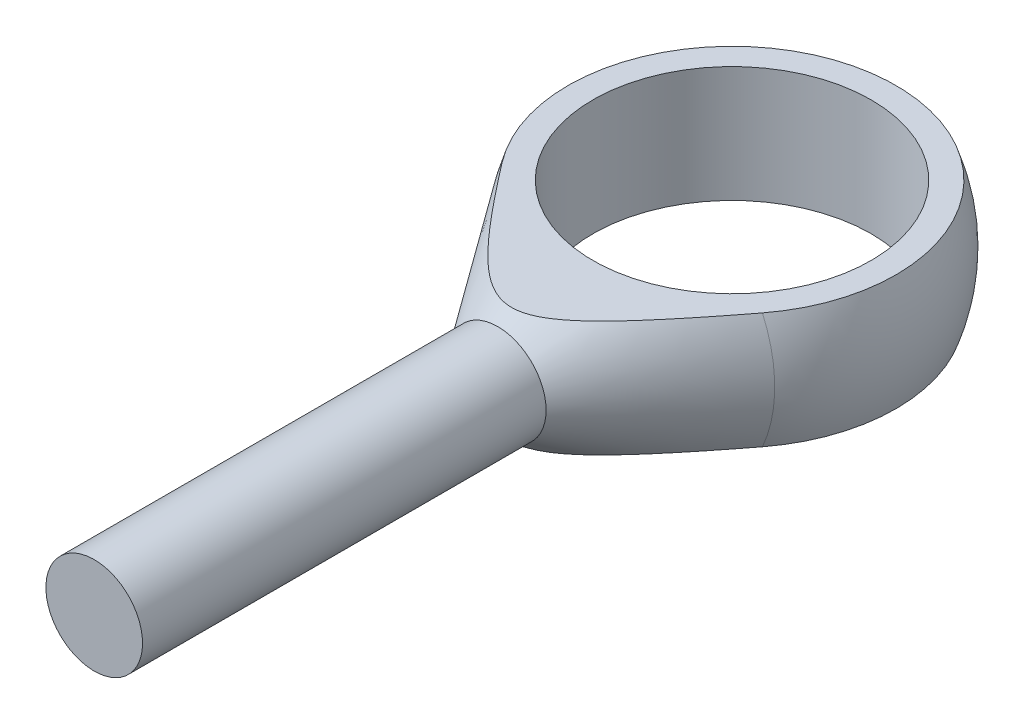
SolidWorks part; units mm, degrees
ref_plane "Front Plane" through (0, 0, 0) normal (0, 0, 1) x (1, 0, 0)
ref_plane "Top Plane" through (0, 0, 0) normal (0, 1, 0) x (1, 0, 0)
ref_plane "Right Plane" through (0, 0, 0) normal (1, 0, 0) x (0, 0, -1)
sketch "Sketch1" plane through (0, 0, 0) normal (0, 0, 1) x (1, 0, 0)
  line L0 (-8.4853, 3) -> (-7.2, 3)
  line L1 (-7.2, 3) -> (-7.2, -3)
  line L2 (-7.2, -3) -> (-8.4853, -3)
  line L3 (0, 0) -> (-7.2, 3) construction
  line L4 (0, -4.3877) -> (0, 5.0326) construction
  arc A0 (-8.4853, 3) -> (-8.4853, -3) centre (0, 0) ccw
  point P5 (-7.2, 0)
  dimension "D1" = 18
  dimension "D2" = 6
  dimension "D3" = 7.8
revolve "Revolve1" add sketch "Sketch1" angle 360 about L4
ref_plane "Plane1" through (0, 0, 0) normal (0, 1, 0) x (1, 0, 0)
sketch "Sketch3" plane through (0, 0, 0) normal (0, 1, 0) x (1, 0, 0)
  line L0 (0, 0) -> (0, -33) construction
  dimension "D1" = 33
ref_plane "Plane2" through (0, 0, 33) normal (0, 0, 1) x (1, 0, 0)
sketch "Sketch4" plane through (0, 0, 33) normal (0, 0, 1) x (1, 0, 0)
  circle A0 centre (0, 0) radius 2.5
  dimension "D1" = 5
extrude "Boss-Extrude1" add sketch "Sketch4" against normal up to surface (24.3542 mm away)
sketch "Sketch5" plane through (0, 0, 0) normal (0, 1, 0) x (1, 0, 0)
  line L0 (0, -7.8) -> (0, -15.691)
  line L1 (0, 0) -> (0, -33) construction
  line L2 (0, -15.691) -> (-7.3724, -5.1622)
  line L3 (-7.8, 0) -> (-9, 0)
  arc A0 (-9, 0) -> (-7.3724, -5.1622) centre (0, 0) ccw
  arc A1 (-7.8, 0) -> (0, -7.8) centre (0, 0) ccw
  dimension "D1" = 18
  dimension "D2" = 15.6
  dimension "D3" = 35
revolve "Revolve2" add sketch "Sketch5" angle 360 about L0
ref_plane "Plane3" through (0, 0, 0) normal (-1, 0, 0) x (0, 0, 1)
sketch "Sketch6" plane through (0, 0, 0) normal (-1, 0, 0) x (0, 0, 1)
  line L0 (0, 7.8) -> (0, 3) construction
  line L1 (0, 3) -> (11.4066, 3)
  line L2 (0, 3) -> (0, 13)
  line L3 (0, 13) -> (12, 13)
  line L4 (12, 3) -> (12, 13)
  line L5 (0, -3) -> (0, -9) construction
  line L6 (0, -3) -> (11.4066, -3)
  line L7 (0, -3) -> (0, -13)
  line L8 (0, -13) -> (12, -13)
  line L9 (12, -3) -> (12, -13)
  line L10 (-1.164, 0) -> (10.1604, 0) construction
  line L11 (4.6669, 0) -> (-4.6669, 0) construction
  line L12 (0, 0) -> (33, 0) construction
  line L13 (11.4066, -3) -> (12.1207, -2.5)
  line L14 (5.1622, -7.3724) -> (12.1207, -2.5) construction
  line L15 (12.1207, -2.5) -> (12, -3)
  line L16 (12, 3) -> (12.1207, 2.5)
  line L17 (12.1207, 2.5) -> (11.4066, 3)
  line L18 (12.1207, 2.5) -> (5.1622, 7.3724) construction
  dimension "D1" = 12
  dimension "D2" = 12
  dimension "D3" = 10
  dimension "D4" = 3
  dimension "D5" = 3
  dimension "D6" = 10
extrude "Cut-Extrude1" cut sketch "Sketch6" against normal through all both and the other way through all
